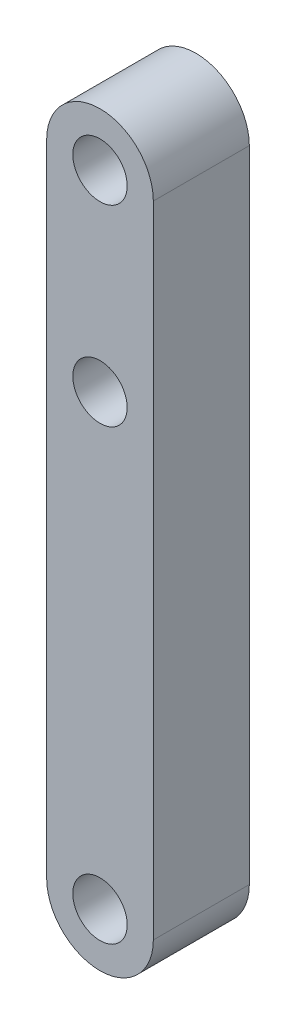
SolidWorks part; units mm, degrees
ref_plane "Front Plane" through (0, 0, 0) normal (0, 0, 1) x (1, 0, 0)
ref_plane "Top Plane" through (0, 0, 0) normal (0, 1, 0) x (1, 0, 0)
ref_plane "Right Plane" through (0, 0, 0) normal (1, 0, 0) x (0, 0, -1)
sketch "Sketch1" plane through (0, 0, 0) normal (0, 0, 1) x (1, 0, 0)
  line L2 (-5, 0) -> (-5, -60)
  line L4 (5, 0) -> (5, -60)
  arc A0 (5, 0) -> (-5, 0) centre (0, 0) ccw
  arc A1 (-5, -60) -> (5, -60) centre (0, -60) ccw
  dimension "D2" = 10
  dimension "D1" = 60
extrude "Boss-Extrude1" add sketch "Sketch1" along normal blind 9
ref_plane "Plane1" through (0, 0, 9) normal (0, 0, 1) x (1, 0, 0)
sketch "Sketch2" plane through (0, 0, 9) normal (0, 0, 1) x (1, 0, 0)
  circle A0 centre (0, 0) radius 2.55
  circle A1 centre (0, -60) radius 2.55
  arc A2 (-5, -60) -> (5, -60) centre (0, -60) ccw construction
  circle A3 centre (0, -18) radius 2.55
  dimension "D1" = 5.1
  dimension "D3" = 18
extrude "Cut-Extrude1" cut sketch "Sketch2" against normal through all
